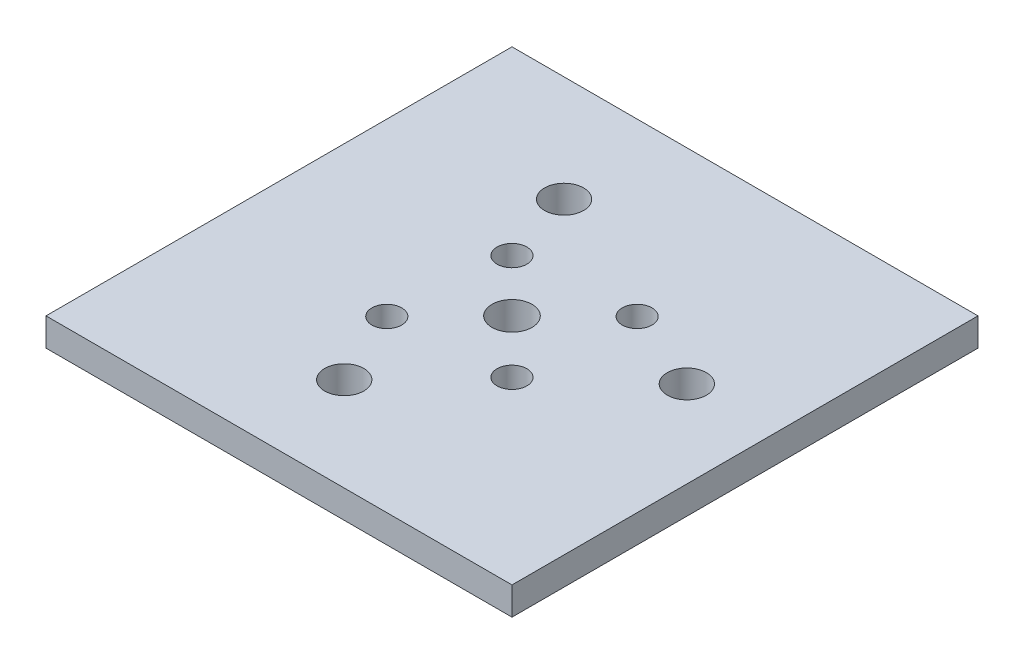
SolidWorks part; units mm, degrees
ref_plane "Front Plane" through (0, 0, 0) normal (0, 0, 1) x (1, 0, 0)
ref_plane "Top Plane" through (0, 0, 0) normal (0, 1, 0) x (1, 0, 0)
ref_plane "Right Plane" through (0, 0, 0) normal (1, 0, 0) x (0, 0, -1)
sketch "Sketch1" plane through (0, 0, 0) normal (0, 1, 0) x (1, 0, 0)
  line L1 (-25, 25) -> (25, 25)
  line L2 (-25, 25) -> (-25, -25)
  line L3 (-25, -25) -> (25, -25)
  line L4 (25, 25) -> (25, -25)
  line L5 (-25, 25) -> (25, -25) construction
  line L6 (-25, -25) -> (25, 25) construction
  point P0 (0, 0)
  dimension "D1" = 50
  dimension "D2" = 50
extrude "Boss-Extrude1" add sketch "Sketch1" against normal blind 3
sketch "Sketch2" plane through (0, 0, 0) normal (0, 1, 0) x (1, 0, 0)
  circle A0 centre (0, 0) radius 2.15
  dimension "D1" = 4.3
extrude "Cut-Extrude1" cut sketch "Sketch2" against normal through all
sketch "Sketch3" plane through (0, 0, 0) normal (0, 1, 0) x (1, 0, 0)
  circle A0 centre (6.7684, 6.6571) radius 1.6
  circle A1 centre (-6.6616, -6.7729) radius 1.6
  circle A2 centre (-5.6016, 5.5971) radius 1.6
  circle A3 centre (5.7084, -5.7129) radius 1.6
  dimension "D1" = 3.2
  dimension "D3" = 3.2
  dimension "D5" = 3.2
  dimension "D7" = 3.2
  dimension "D2" = 12.37
  dimension "D4" = 1.06
  dimension "D6" = 12.37
  dimension "D9" = 1.06
  dimension "D10" = 12.37
  dimension "D11" = 1.06
extrude "Cut-Extrude2" cut sketch "Sketch3" against normal through all
sketch "Sketch4" plane through (0, 0, 0) normal (0, 1, 0) x (1, 0, 0)
  circle A0 centre (15.7054, 3.0563) radius 2.1
  circle A1 centre (-3.0643, -14.9353) radius 2.1
  circle A2 centre (-8.0458, 13.6337) radius 2.1
  dimension "D1" = 16
  dimension "D2" = 29
  dimension "D3" = 26
  dimension "D5" = 26
extrude "Cut-Extrude3" cut sketch "Sketch4" against normal through all
